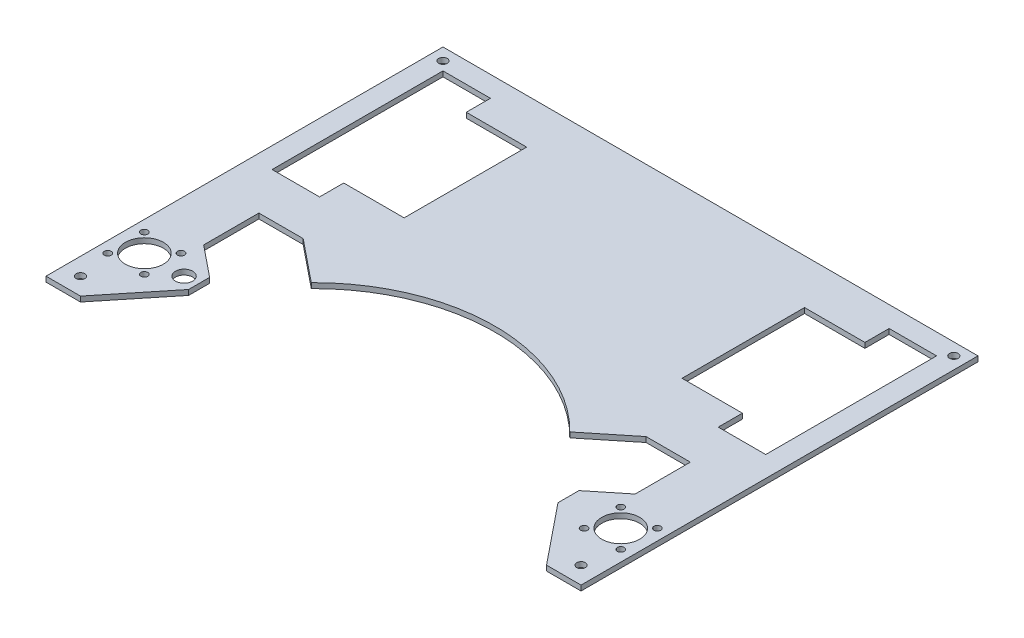
SolidWorks part; units mm, degrees
ref_plane "Face" through (0, 0, 0) normal (0, 0, 1) x (1, 0, 0)
ref_plane "Dessus" through (0, 0, 0) normal (0, 1, 0) x (1, 0, 0)
ref_plane "Droite" through (0, 0, 0) normal (1, 0, 0) x (0, 0, -1)
sketch "Esquisse1" plane through (0, 0, 0) normal (0, 1, 0) x (1, 0, 0)
  line L0 (155, 0) -> (-155, 0)
  line L1 (-155, 0) -> (-155, -230)
  line L2 (-155, -230) -> (-135, -230)
  line L3 (0, 0) -> (0, -230) construction
  line L4 (-155, -230) -> (155, -230) construction
  line L5 (-80.5, -26) -> (-115.5, -26)
  line L6 (-143, -12) -> (-143, -111)
  line L7 (-115.5, -26) -> (-115.5, -12)
  line L8 (-80.5, -26) -> (-80.5, -97)
  line L9 (115.5, -26) -> (115.5, -12)
  line L10 (115.5, -12) -> (143, -12)
  line L11 (80.5, -26) -> (115.5, -26)
  line L12 (80.5, -26) -> (80.5, -97)
  line L13 (80.5, -97) -> (115.5, -97)
  line L14 (155, -230) -> (135, -230)
  line L15 (155, 0) -> (155, -230)
  line L16 (-138, -179) -> (-138, -201) construction
  line L17 (-135, -230) -> (-107, -195.3518)
  line L18 (-107, -195.3518) -> (-107, -183.1958)
  line L19 (-149, -190) -> (-127, -190) construction
  line L20 (-138, -190) -> (-149, -179) construction
  line L21 (-149, -190) -> (-149, -179) construction
  line L22 (-149, -179) -> (-138, -179) construction
  line L23 (-155, -210) -> (-118.8376, -210) construction
  line L24 (-107, -183.1958) -> (-125, -168.6496)
  line L25 (-125, -168.6496) -> (-125, -136.6496)
  line L26 (135, -230) -> (107, -195.3518)
  line L27 (107, -195.3518) -> (107, -183.1958)
  line L28 (-125, -136.6496) -> (-99.3345, -136.6496)
  line L29 (-115.5, -12) -> (-143, -12)
  line L30 (-80.5, -97) -> (-115.5, -97)
  line L31 (-115.5, -97) -> (-115.5, -111)
  line L32 (-115.5, -111) -> (-143, -111)
  line L33 (115.5, -97) -> (115.5, -111)
  line L34 (115.5, -111) -> (143, -111)
  line L35 (143, -12) -> (143, -111)
  line L36 (-99.3345, -136.6496) -> (-74.8903, -156.4035)
  line L37 (-127, -190) -> (-115, -190) construction
  line L38 (99.3345, -136.6496) -> (74.8903, -156.4035)
  line L39 (125, -136.6496) -> (99.3345, -136.6496)
  line L40 (125, -168.6496) -> (125, -136.6496)
  line L41 (107, -183.1958) -> (125, -168.6496)
  arc A0 (-74.8903, -156.4035) -> (74.8903, -156.4035) centre (0, -230) cw
  circle A1 centre (-148, -7) radius 2.5
  circle A2 centre (148, -7) radius 2.5
  circle A3 centre (-145, -220) radius 2.5
  circle A4 centre (145, -220) radius 2.5
  circle A5 centre (-138, -190) radius 11
  circle A6 centre (-148.6066, -179.3934) radius 2
  circle A7 centre (-127.3934, -179.3934) radius 2
  circle A8 centre (-127.3934, -200.6066) radius 2
  circle A9 centre (-148.6066, -200.6066) radius 2
  circle A10 centre (138, -190) radius 11
  circle A11 centre (148.6066, -200.6066) radius 2
  circle A12 centre (127.3934, -200.6066) radius 2
  circle A13 centre (127.3934, -179.3934) radius 2
  circle A14 centre (148.6066, -179.3934) radius 2
  circle A15 centre (-115, -190) radius 5
  dimension "D3" = 20
  dimension "D9" = 5
  dimension "D10" = 105
  dimension "D13" = 5
  dimension "D16" = 22
  dimension "D18" = 4
  dimension "D25" = 10
  dimension "D1" = 155
  dimension "D2" = 230
  dimension "D4" = 26
  dimension "D5" = 14
  dimension "D6" = 80.5
  dimension "D7" = 12
  dimension "D8" = 71
  dimension "D11" = 7
  dimension "D12" = 7
  dimension "D14" = 10
  dimension "D15" = 10
  dimension "D17" = 17
  dimension "D19" = 15
  dimension "D20" = 40
  dimension "D21" = 10
  dimension "D22" = 48
  dimension "D23" = 30
  dimension "D24" = 27.5
  dimension "D26" = 23
  dimension "D27" = 32
extrude "Extrusion1" add sketch "Esquisse1" along normal blind 3
